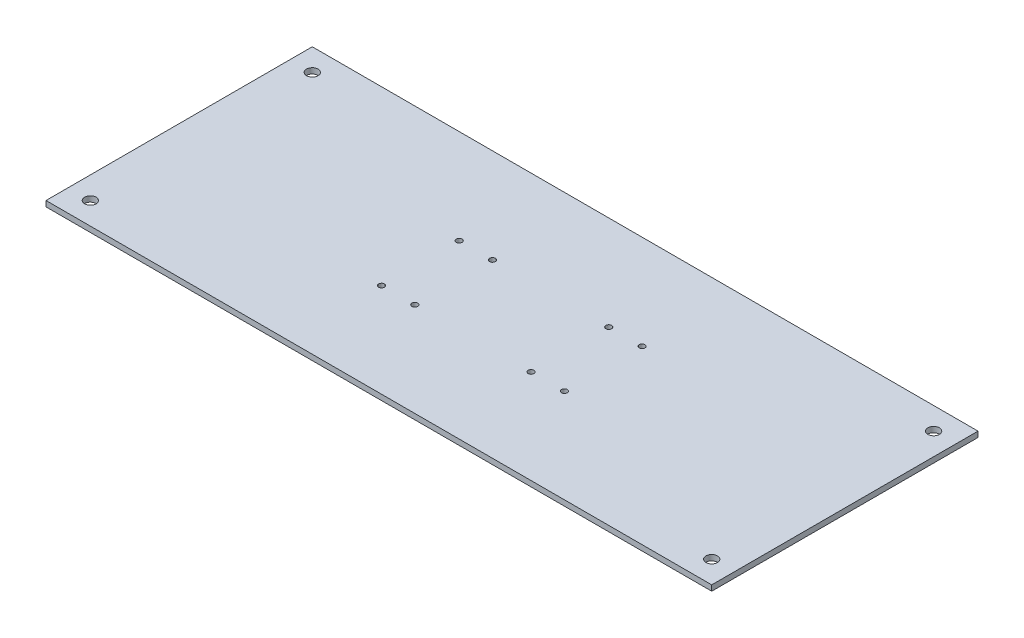
SolidWorks part; units mm, degrees
ref_plane "Front" through (0, 0, 0) normal (0, 0, 1) x (1, 0, 0)
ref_plane "Top" through (0, 0, 0) normal (0, 1, 0) x (1, 0, 0)
ref_plane "Right" through (0, 0, 0) normal (1, 0, 0) x (0, 0, -1)
sketch "Sketch1" plane through (0, 0, 0) normal (0, 1, 0) x (1, 0, 0)
  line L0 (0, 76.2) -> (0, -76.2) construction
  line L1 (-190.5, 76.2) -> (190.5, 76.2)
  line L2 (-190.5, 76.2) -> (-190.5, -76.2)
  line L3 (-190.5, -76.2) -> (190.5, -76.2)
  line L4 (190.5, 76.2) -> (190.5, -76.2)
  line L5 (-190.5, 0) -> (190.5, 0) construction
  line L7 (-52.324, 22.098) -> (-33.274, 22.098) construction
  line L8 (-52.324, 22.098) -> (-52.324, -22.352) construction
  line L9 (-52.324, -22.352) -> (-33.274, -22.352) construction
  line L10 (-33.274, 22.098) -> (-33.274, -22.352) construction
  circle A0 centre (-177.8, 63.5) radius 3.302
  circle A1 centre (177.8, 63.5) radius 3.302
  circle A2 centre (-177.8, -63.5) radius 3.302
  circle A3 centre (177.8, -63.5) radius 3.302
  circle A4 centre (-52.324, 22.098) radius 1.651
  circle A5 centre (-52.324, -22.352) radius 1.651
  circle A6 centre (-33.274, 22.098) radius 1.651
  circle A7 centre (-33.274, -22.352) radius 1.651
  circle A8 centre (33.274, 22.098) radius 1.651
  circle A9 centre (33.274, -22.352) radius 1.651
  circle A10 centre (52.324, -22.352) radius 1.651
  circle A11 centre (52.324, 22.098) radius 1.651
  point P4 (0, 76.2)
  point P6 (-190.5, 0)
  dimension "D5" = 6.604
  dimension "D7" = 3.302
  dimension "D1" = 381
  dimension "D2" = 152.4
  dimension "D3" = 12.7
  dimension "D4" = 12.7
  dimension "D6" = 138.176
  dimension "D8" = 54.102
  dimension "D9" = 44.45
  dimension "D10" = 19.05
extrude "Boss-Extrude1" add sketch "Sketch1" along normal blind 3.175
